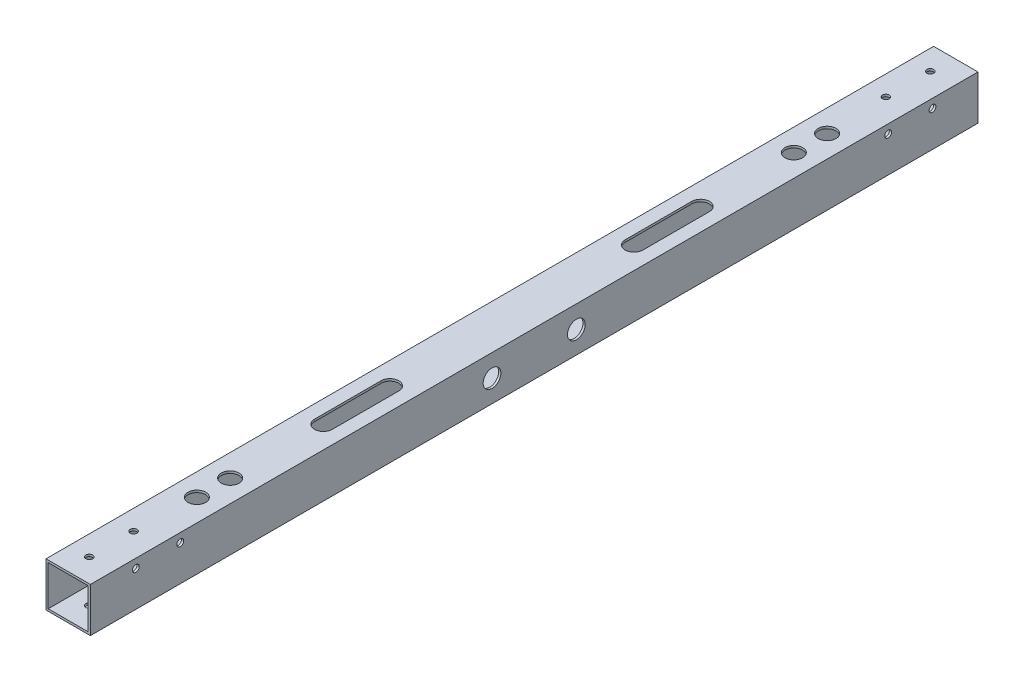
SolidWorks part; units mm, degrees
material "6063-T5"
ref_plane "前视基准面" through (0, 0, 0) normal (0, 0, 1) x (1, 0, 0)
ref_plane "上视基准面" through (0, 0, 0) normal (0, 1, 0) x (1, 0, 0)
ref_plane "右视基准面" through (0, 0, 0) normal (1, 0, 0) x (0, 0, -1)
other "Configuration Table"
sketch "草图1" plane through (0, 0, 0) normal (0, 0, 1) x (1, 0, 0)
  line L1 (-10, -10) -> (10, -10)
  line L2 (-10, -10) -> (-10, 10)
  line L3 (-10, 10) -> (10, 10)
  line L4 (10, -10) -> (10, 10)
  line L5 (-10, -10) -> (10, 10) construction
  line L6 (-10, 10) -> (10, -10) construction
  point P0 (0, 0)
  dimension "D1" = 20
  dimension "D2" = 20
extrude "凸台-拉伸1" add sketch "草图1" along normal mid plane 400
sketch "草图2" plane through (0, 0, 0) normal (0, 0, 1) x (1, 0, 0)
  line L8 (9, -9) -> (9, 9)
  line L9 (9, 9) -> (-9, 9)
  line L10 (-9, 9) -> (-9, -9)
  line L11 (-9, -9) -> (9, -9)
  line L12 (9, -9) -> (9, 9)
  line L13 (9, 9) -> (-9, 9)
  line L14 (-9, 9) -> (-9, -9)
  line L15 (-9, -9) -> (9, -9)
  dimension "D1" = 1
extrude "切除-拉伸1" cut sketch "草图2" against normal through all both and the other way through all
sketch "草图3" plane through (0, 10, 0) normal (0, 1, 0) x (1, 0, 0)
  line L0 (10, -200) -> (-10, -200) construction
  circle A0 centre (-1, -189.5) radius 1.525
  circle A1 centre (-1, -169.5) radius 1.525
  dimension "D1" = 3.05
  dimension "D3" = 10.5
extrude "切除-拉伸2" cut sketch "草图3" against normal through all both and the other way through all
mirror "镜向1" about plane through (0, 0, 0) normal (0, 0, 1) of "切除-拉伸2"
sketch "草图4" plane through (10, 0, 0) normal (1, 0, 0) x (0, 0, -1)
  line L0 (0, 0) -> (0, 10) construction
  line L1 (-200, 10) -> (200, 10) construction
  line L2 (-200, -10) -> (200, -10) construction
  circle A0 centre (-19, 0) radius 2.025
  circle A1 centre (19, 0) radius 2.025
  dimension "D1" = 38
  dimension "D3" = 4.05
  dimension "D2" = 10
extrude "切除-拉伸3" cut sketch "草图4" against normal through all
sketch "草图5" plane through (10, 0, 0) normal (1, 0, 0) x (0, 0, -1)
  circle A0 centre (-19, 0) radius 4
  circle A1 centre (19, 0) radius 4
  dimension "D1" = 8
extrude "切除-拉伸4" cut sketch "草图5" against normal up to surface (1 mm away) up to face at (9, 0, 16.975)
sketch "草图6" plane through (10, 0, 0) normal (1, 0, 0) x (0, 0, -1)
  line L0 (200, -10) -> (200, 10) construction
  line L5 (200, -10) -> (200, 10)
  line L6 (200, 10) -> (-200, 10)
  line L7 (-200, 10) -> (-200, -10)
  line L8 (-200, -10) -> (200, -10)
  line L9 (200, -10) -> (200, 10)
  line L10 (200, 10) -> (-200, 10)
  line L11 (-200, 10) -> (-200, -10)
  line L12 (-200, -10) -> (200, -10)
  circle A0 centre (159.5, 6) radius 1.525
  circle A1 centre (179.5, 6) radius 1.525
  dimension "D1" = 3.05
  dimension "D2" = 20.5
  dimension "D3" = 20
  dimension "D5" = 4
  dimension "D4" = 0
extrude "切除-拉伸5" cut sketch "草图6" against normal through all both contours A0 | A1
sketch "草图7" plane through (0, 10, 0) normal (0, 1, 0) x (1, 0, 0)
  line L0 (0, 0) -> (-10, 0) construction
  line L1 (-10, -200) -> (-10, 200) construction
  line L2 (10, 200) -> (-10, 200) construction
  circle A0 centre (0, 142) radius 2.025
  circle A1 centre (0, 127) radius 2.025
  circle A4 centre (0, -127) radius 2.025
  circle A5 centre (0, -142) radius 2.025
  dimension "D1" = 4.05
  dimension "D3" = 10
  dimension "D4" = 58
  dimension "D2" = 15
extrude "切除-拉伸6" cut sketch "草图7" against normal through all both and the other way through all
sketch "草图8" plane through (0, 10, 0) normal (0, 1, 0) x (1, 0, 0)
  line L0 (0, 0) -> (-10, 0) construction
  line L1 (-10, -200) -> (-10, 200) construction
  circle A0 centre (0, 142) radius 4
  circle A1 centre (0, 127) radius 4
  circle A2 centre (0, -127) radius 4
  circle A3 centre (0, -142) radius 4
  dimension "D1" = 8
extrude "切除-拉伸7" cut sketch "草图8" against normal blind 3
mirror "镜向2" about plane through (0, 0, 0) normal (0, 0, 1) of "切除-拉伸5"
sketch "草图9" plane through (0, 10, 0) normal (0, 1, 0) x (1, 0, 0)
  line L0 (0, 85) -> (0, 55) construction
  line L1 (4, 85) -> (4, 55)
  line L2 (-4, 85) -> (-4, 55)
  line L3 (0, 0) -> (-10, 0) construction
  line L4 (-10, -200) -> (-10, 200) construction
  line L5 (0, -85) -> (0, -55) construction
  line L6 (4, -85) -> (4, -55)
  line L7 (-4, -85) -> (-4, -55)
  arc A0 (4, 85) -> (-4, 85) centre (0, 85) ccw
  arc A1 (-4, 55) -> (4, 55) centre (0, 55) ccw
  arc A2 (4, -85) -> (-4, -85) centre (0, -85) cw
  arc A3 (-4, -55) -> (4, -55) centre (0, -55) cw
  point P3 (0, 70)
  point P14 (0, -70)
  dimension "D1" = 4
  dimension "D2" = 30
  dimension "D3" = 70
extrude "切除-拉伸8" cut sketch "草图9" against normal through all both and the other way through all
